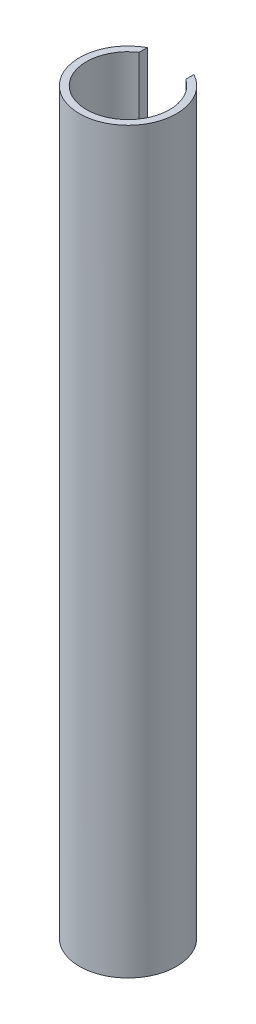
SolidWorks part; units mm, degrees
material "Полипропиленовая пленка"
ref_plane "Спереди" through (0, 0, 0) normal (0, 0, 1) x (1, 0, 0)
ref_plane "Сверху" through (0, 0, 0) normal (0, 1, 0) x (1, 0, 0)
ref_plane "Справа" through (0, 0, 0) normal (1, 0, 0) x (0, 0, -1)
sketch "Эскиз1" plane through (0, 0, 0) normal (0, 1, 0) x (1, 0, 0)
  circle A0 centre (0, 0) radius 12.5
  circle A1 centre (0, 0) radius 10.7
  dimension "D1" = 25
  dimension "D2" = 21.4
extrude "Бобышка-Вытянуть1" add sketch "Эскиз1" along normal blind 190
sketch "Эскиз3" plane through (0, 190, 0) normal (0, 1, 0) x (1, 0, 0)
  line L1 (-6, 12.8144) -> (6, 12.8144)
  line L2 (-6, 12.8144) -> (-6, 8)
  line L3 (-6, 8) -> (6, 8)
  line L4 (6, 12.8144) -> (6, 8)
  point P4 (0, 8)
  dimension "D1" = 12
  dimension "D2" = 8
extrude "Вырез-Вытянуть1" cut sketch "Эскиз3" against normal blind 50
